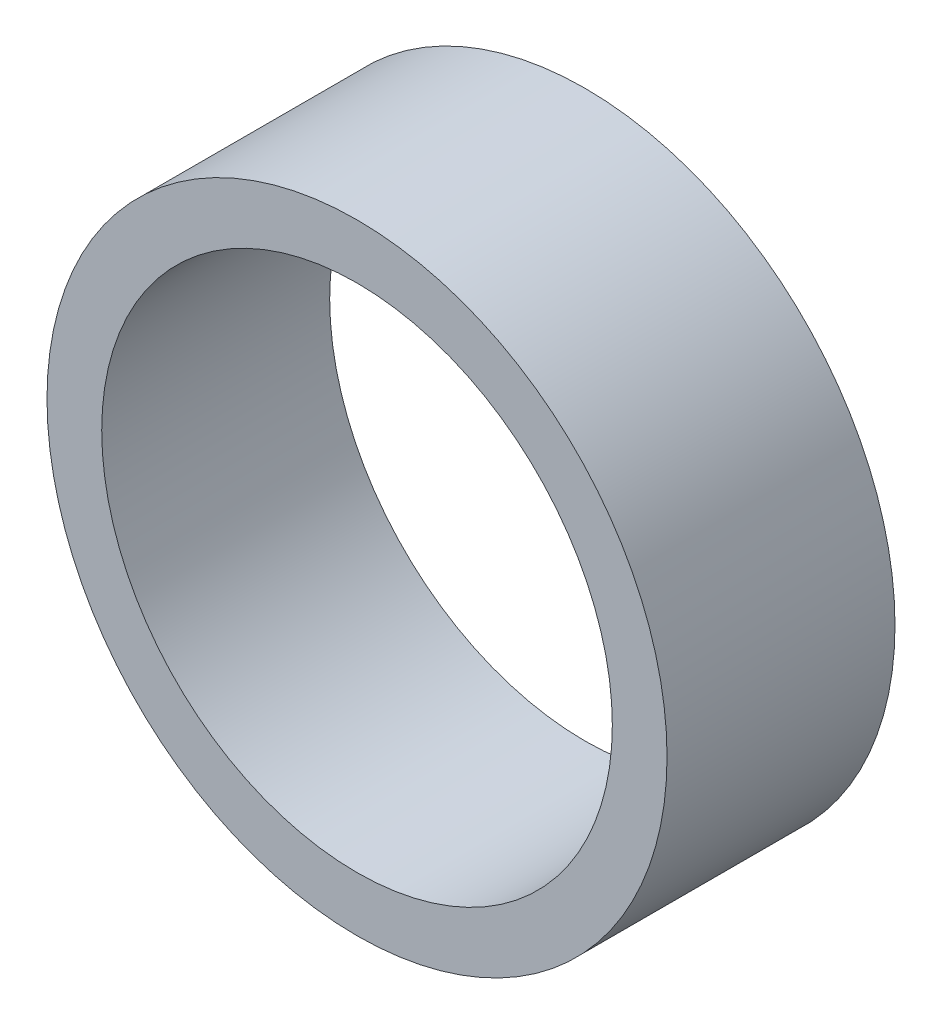
SolidWorks part; units mm, degrees
ref_plane "Front Plane" through (0, 0, 0) normal (0, 0, 1) x (1, 0, 0)
ref_plane "Top Plane" through (0, 0, 0) normal (0, 1, 0) x (1, 0, 0)
ref_plane "Right Plane" through (0, 0, 0) normal (1, 0, 0) x (0, 0, -1)
sketch "Sketch1" plane through (0, 0, 0) normal (0, 0, 1) x (1, 0, 0)
  circle A0 centre (0, 0) radius 11.2
  circle A1 centre (0, 0) radius 13.6
  dimension "D1" = 22.4
  dimension "D2" = 2.4
extrude "Boss-Extrude1" add sketch "Sketch1" along normal blind 10
